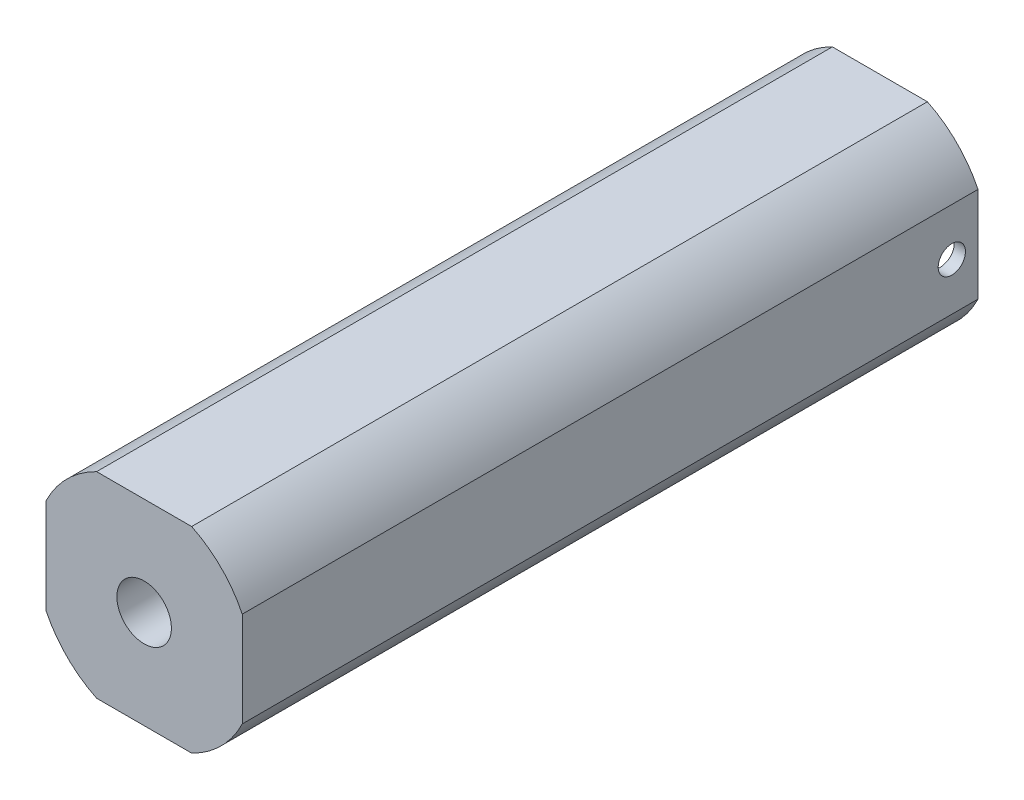
SolidWorks part; units mm, degrees
material "6061-T6 Al"
ref_plane "Front" through (0, 0, 0) normal (0, 0, 1) x (1, 0, 0)
ref_plane "Top" through (0, 0, 0) normal (0, 1, 0) x (1, 0, 0)
ref_plane "Right" through (0, 0, 0) normal (1, 0, 0) x (0, 0, -1)
sketch "Sketch1" plane through (0, 0, 0) normal (0, 0, 1) x (1, 0, 0)
  line L0 (0, 0) -> (0, 5.715) construction
  line L1 (-2.7679, 5.715) -> (2.7679, 5.715)
  line L2 (-5.715, 2.7679) -> (-5.715, -2.7679)
  line L3 (-2.7679, -5.715) -> (2.7679, -5.715)
  line L4 (5.715, 2.7679) -> (5.715, -2.7679)
  line L5 (0, 0) -> (5.715, 0) construction
  arc A0 (-2.7679, 5.715) -> (-5.715, 2.7679) centre (0, 0) ccw
  arc A1 (-5.715, -2.7679) -> (-2.7679, -5.715) centre (0, 0) ccw
  arc A2 (5.715, 2.7679) -> (2.7679, 5.715) centre (0, 0) ccw
  arc A3 (2.7679, -5.715) -> (5.715, -2.7679) centre (0, 0) ccw
  point P0 (-5.715, 5.715)
  point P1 (5.715, -5.715)
  point P2 (-5.715, -5.715)
  point P3 (5.715, 5.715)
  point P18 (5.715, 5.715)
  point P21 (-5.715, -5.715)
  dimension "D2" = 12.7
  dimension "D1" = 11.43
  dimension "D3" = 5.715
  dimension "D4" = 5.715
  dimension "D5" = 5.715
extrude "Boss-Extrude1" add sketch "Sketch1" along normal blind 42.8498
cosmetic thread "Cosmetic Thread1" parameters "D2"=11.7
sketch "Sketch4" plane through (0, 0, 0) normal (0, 0, -1) x (-1, 0, 0)
  circle A0 centre (0, 0) radius 5.05
  dimension "D1" = 10.1
extrude "Cut-Extrude1" cut sketch "Sketch4" against normal blind 1.524
hole_wizard "1/16 (0.0625) Diameter Hole1" positions "Sketch10" profile "Sketch11" hole size "1/16" standard "Ansi Inch" end condition through all
sketch "Sketch10" plane through (5.715, 0, 0) normal (1, 0, 0) x (0, 0, -1)
  line L0 (0, 0) -> (-1.524, 0) construction
  point P0 (-1.524, 0)
  dimension "D1" = 1.524
sketch "Sketch11" plane through (5.715, 0, 1.524) normal (0, 1, 0) x (0, 0, -1)
  line L0 (0, 0) -> (0, 11.43)
  line L1 (0, 11.43) -> (0.7937, 11.43)
  line L2 (0.7937, 11.43) -> (0.7937, 0)
  line L5 (0.7937, 0) -> (0, 0)
  line L11 (0, -6.35) -> (0, 107.95) construction
  dimension "Thru Hole Dia." = 1.5875
  dimension "Thru Hole Depth" = 11.43
hole_wizard "1/8 (0.125) Diameter Hole2" positions "Sketch13" profile "Sketch14" hole size "1/8" standard "Ansi Inch" end condition through all
sketch "Sketch13" plane through (0, 0, 1.524) normal (0, 0, -1) x (-1, 0, 0)
  point P0 (0, 0)
sketch "Sketch14" plane through (0, 0, 1.524) normal (1, 0, 0) x (0, 1, 0)
  line L0 (0, 0) -> (0, 41.3258)
  line L1 (0, 41.3258) -> (1.5875, 41.3258)
  line L2 (1.5875, 41.3258) -> (1.5875, 0)
  line L5 (1.5875, 0) -> (0, 0)
  line L11 (0, -6.35) -> (0, 107.95) construction
  dimension "Thru Hole Dia." = 3.175
  dimension "Thru Hole Depth" = 41.3258
